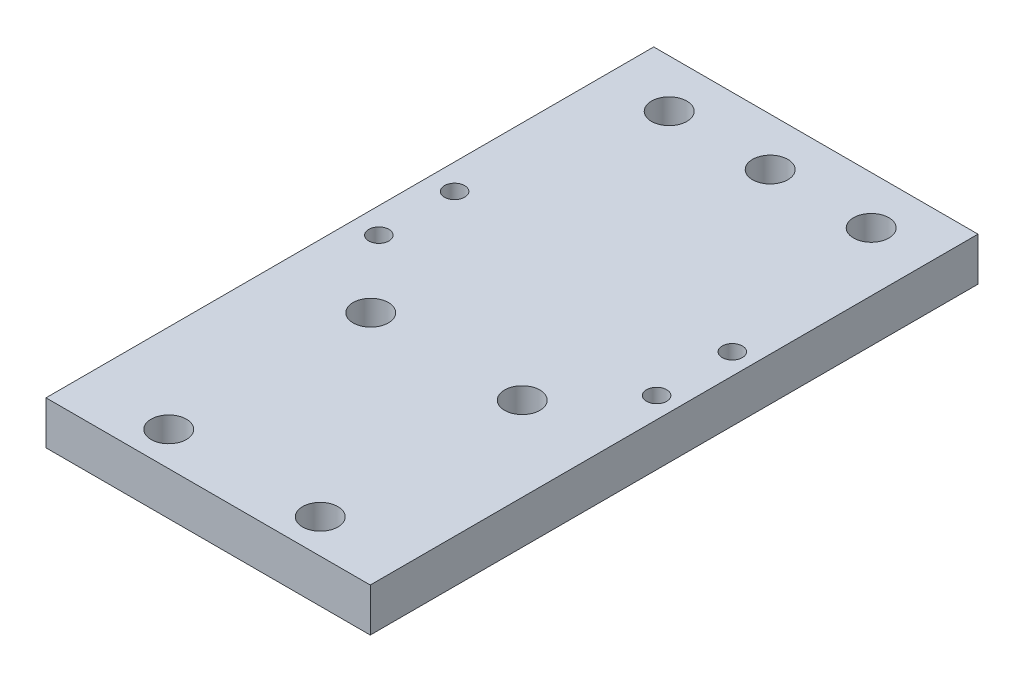
SolidWorks part; units mm, degrees
ref_plane "Front Plane" through (0, 0, 0) normal (0, 0, 1) x (1, 0, 0)
ref_plane "Top Plane" through (0, 0, 0) normal (0, 1, 0) x (1, 0, 0)
ref_plane "Right Plane" through (0, 0, 0) normal (1, 0, 0) x (0, 0, -1)
sketch "Sketch1" plane through (0, 0, 0) normal (0, 1, 0) x (1, 0, 0)
  line L0 (0, -23.4565) -> (0, 53.3719) construction
  line L6 (-16.0528, 60.1726) -> (16.0528, 60.1726)
  line L7 (-16.0528, 60.1726) -> (-16.0528, 0)
  line L8 (-16.0528, 0) -> (16.0528, 0)
  line L9 (16.0528, 60.1726) -> (16.0528, 0)
  line L10 (-16.0528, 60.1726) -> (16.0528, 0) construction
  line L11 (-16.0528, 0) -> (16.0528, 60.1726) construction
  point P3 (0, 30.0863)
  dimension "D1" = 32.1056
  dimension "D2" = 60.1726
extrude "Boss-Extrude1" add sketch "Sketch1" along normal blind 4.2926
sketch "Sketch2" plane through (0, 4.2926, 0) normal (0, 1, 0) x (1, 0, 0)
  line L0 (-9.7722, 55.4226) -> (10.2278, 55.4226) construction
  line L1 (0.2278, -14.7291) -> (0.2278, 58.7438) construction
  line L2 (-13.5222, 37.9226) -> (13.9778, 37.9226) construction
  line L3 (-13.5222, 37.9226) -> (-13.5222, 30.4226) construction
  line L4 (-13.5222, 30.4226) -> (13.9778, 30.4226) construction
  line L5 (13.9778, 37.9226) -> (13.9778, 30.4226) construction
  line L6 (-13.5222, 37.9226) -> (13.9778, 30.4226) construction
  line L7 (-13.5222, 30.4226) -> (13.9778, 37.9226) construction
  line L8 (-7.2722, 3.3726) -> (7.7278, 3.3726) construction
  line L9 (-7.2722, 3.3726) -> (-7.2722, 23.3726) construction
  line L10 (-7.2722, 23.3726) -> (7.7278, 23.3726) construction
  line L11 (7.7278, 3.3726) -> (7.7278, 23.3726) construction
  line L12 (-7.2722, 3.3726) -> (7.7278, 23.3726) construction
  line L13 (-7.2722, 23.3726) -> (7.7278, 3.3726) construction
  line L16 (16.0528, 60.1726) -> (-16.0528, 60.1726) construction
  circle A0 centre (-9.7722, 55.4226) radius 1.75
  circle A1 centre (0.2278, 55.4226) radius 1.75
  circle A2 centre (10.2278, 55.4226) radius 1.75
  circle A3 centre (-7.2722, 3.3726) radius 1.75
  circle A4 centre (-7.2722, 23.3726) radius 1.75
  circle A5 centre (7.7278, 23.3726) radius 1.75
  circle A6 centre (7.7278, 3.3726) radius 1.75
  circle A7 centre (13.9778, 30.4226) radius 1
  circle A8 centre (13.9778, 37.9226) radius 1
  circle A9 centre (-13.5222, 37.9226) radius 1
  circle A10 centre (-13.5222, 30.4226) radius 1
  point P2 (0.2278, 34.1726)
  point P12 (0.2278, 13.3726)
  point P20 (0.2278, 55.4226)
  dimension "D10" = 3.5
  dimension "D11" = 3.5
  dimension "D12" = 2
  dimension "D1" = 20
  dimension "D2" = 15
  dimension "D3" = 46.8
  dimension "D4" = 7.5
  dimension "D5" = 27.5
  dimension "D6" = 26
  dimension "D7" = 4.75
  dimension "D8" = 20
  dimension "D9" = 10
extrude "Cut-Extrude1" cut sketch "Sketch2" against normal through all
